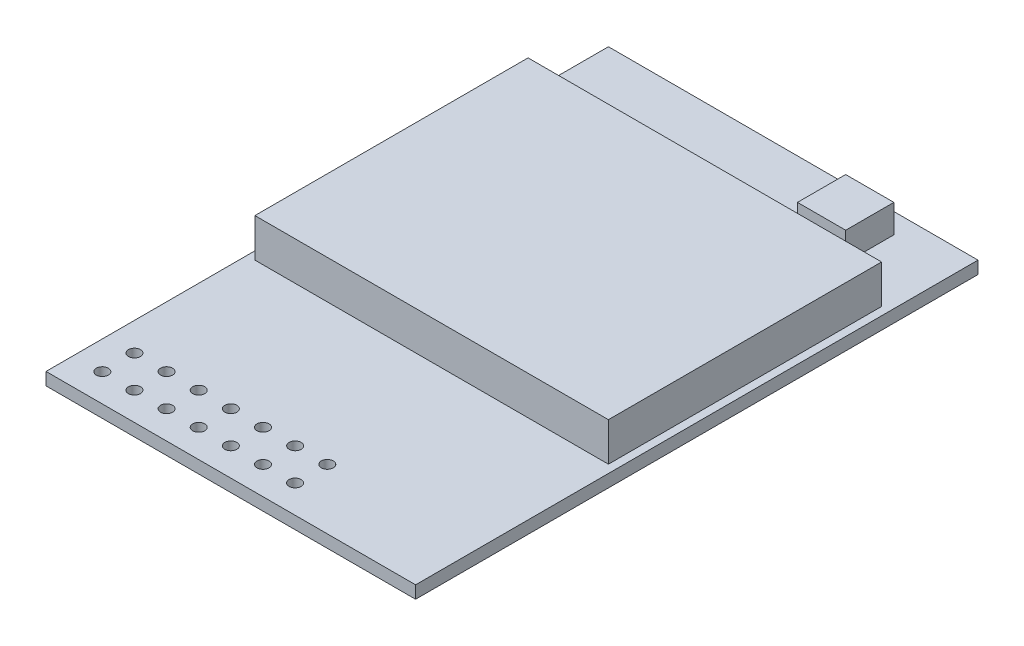
SolidWorks part; units mm, degrees
ref_plane "Front Plane" through (0, 0, 0) normal (0, 0, 1) x (1, 0, 0)
ref_plane "Top Plane" through (0, 0, 0) normal (0, 1, 0) x (1, 0, 0)
ref_plane "Right Plane" through (0, 0, 0) normal (1, 0, 0) x (0, 0, -1)
sketch "Sketch1" plane through (0, 0, 0) normal (0, 1, 0) x (1, 0, 0)
  line L1 (-11.5, -17.5) -> (11.5, -17.5)
  line L2 (-11.5, -17.5) -> (-11.5, 17.5)
  line L3 (-11.5, 17.5) -> (11.5, 17.5)
  line L4 (11.5, -17.5) -> (11.5, 17.5)
  line L5 (-11.5, -17.5) -> (11.5, 17.5) construction
  line L6 (-11.5, 17.5) -> (11.5, -17.5) construction
  point P0 (0, 0)
  dimension "D1" = 23
  dimension "D2" = 35
extrude "Boss-Extrude1" add sketch "Sketch1" along normal blind 0.78
sketch "Sketch2" plane through (0, 0.78, 0) normal (0, 1, 0) x (1, 0, 0)
  line L1 (-11, 12) -> (11, 12)
  line L2 (-11, 12) -> (-11, -5)
  line L3 (-11, -5) -> (11, -5)
  line L4 (11, 12) -> (11, -5)
  line L5 (-11, 12) -> (11, -5) construction
  line L6 (-11, -5) -> (11, 12) construction
  point P0 (0, 3.5)
  point P5 (0, 0)
  dimension "D1" = 22
  dimension "D2" = 17
  dimension "D3" = 3.5
extrude "Boss-Extrude2" add sketch "Sketch2" along normal blind 2.4
sketch "Sketch3" plane through (0, 0.78, 0) normal (0, 1, 0) x (1, 0, 0)
  line L1 (4.5213, 16.2441) -> (7.5213, 16.2441)
  line L2 (4.5213, 16.2441) -> (4.5213, 13.2441)
  line L3 (4.5213, 13.2441) -> (7.5213, 13.2441)
  line L4 (7.5213, 16.2441) -> (7.5213, 13.2441)
  line L5 (4.5213, 16.2441) -> (7.5213, 13.2441) construction
  line L6 (4.5213, 13.2441) -> (7.5213, 16.2441) construction
  point P0 (6.0213, 14.7441)
  point P5 (6.0213, 14.7441)
  dimension "D1" = 3
extrude "Boss-Extrude3" add sketch "Sketch3" along normal blind 1.75
sketch "Sketch4" plane through (0, 0.78, 0) normal (0, 1, 0) x (1, 0, 0)
  circle A0 centre (-9.7369, -15.7591) radius 0.375
  circle A1 centre (-7.7369, -15.7591) radius 0.375
  circle A2 centre (-5.7369, -15.7591) radius 0.375
  circle A3 centre (-3.7369, -15.7591) radius 0.375
  circle A4 centre (-1.7369, -15.7591) radius 0.375
  circle A5 centre (0.2631, -15.7591) radius 0.375
  circle A6 centre (2.2631, -15.7591) radius 0.375
  circle A7 centre (-7.7369, -13.7591) radius 0.375
  circle A8 centre (-5.7369, -13.7591) radius 0.375
  circle A9 centre (-3.7369, -13.7591) radius 0.375
  circle A10 centre (-1.7369, -13.7591) radius 0.375
  circle A11 centre (0.2631, -13.7591) radius 0.375
  circle A12 centre (2.2631, -13.7591) radius 0.375
  circle A13 centre (-9.7369, -13.7591) radius 0.375
  point P2 (-9.7369, -15.7591)
  point P3 (0, 0)
  dimension "D1" = 0.75
  dimension "D2" = 7
  dimension "D3" = 2
extrude "Cut-Extrude1" cut sketch "Sketch4" against normal through all
